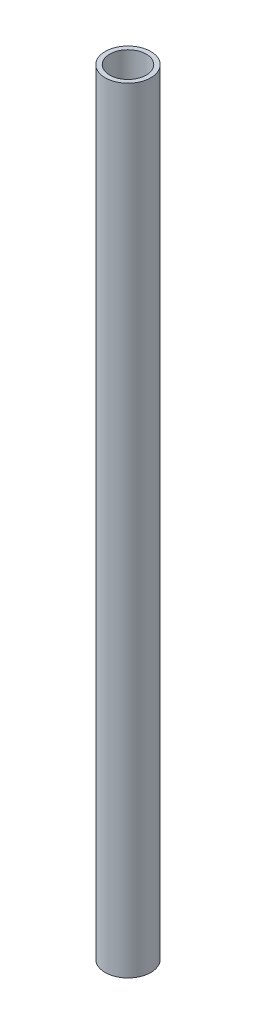
SolidWorks part; units mm, degrees
ref_plane "Front Plane" through (0, 0, 0) normal (0, 0, 1) x (1, 0, 0)
ref_plane "Top Plane" through (0, 0, 0) normal (0, 1, 0) x (1, 0, 0)
ref_plane "Right Plane" through (0, 0, 0) normal (1, 0, 0) x (0, 0, -1)
sketch "Sketch1" plane through (0, 0, 0) normal (0, 1, 0) x (1, 0, 0)
  circle A0 centre (0, 0) radius 4
  circle A1 centre (0, 0) radius 5
extrude "Boss-Extrude1" add sketch "Sketch1" along normal blind 170
